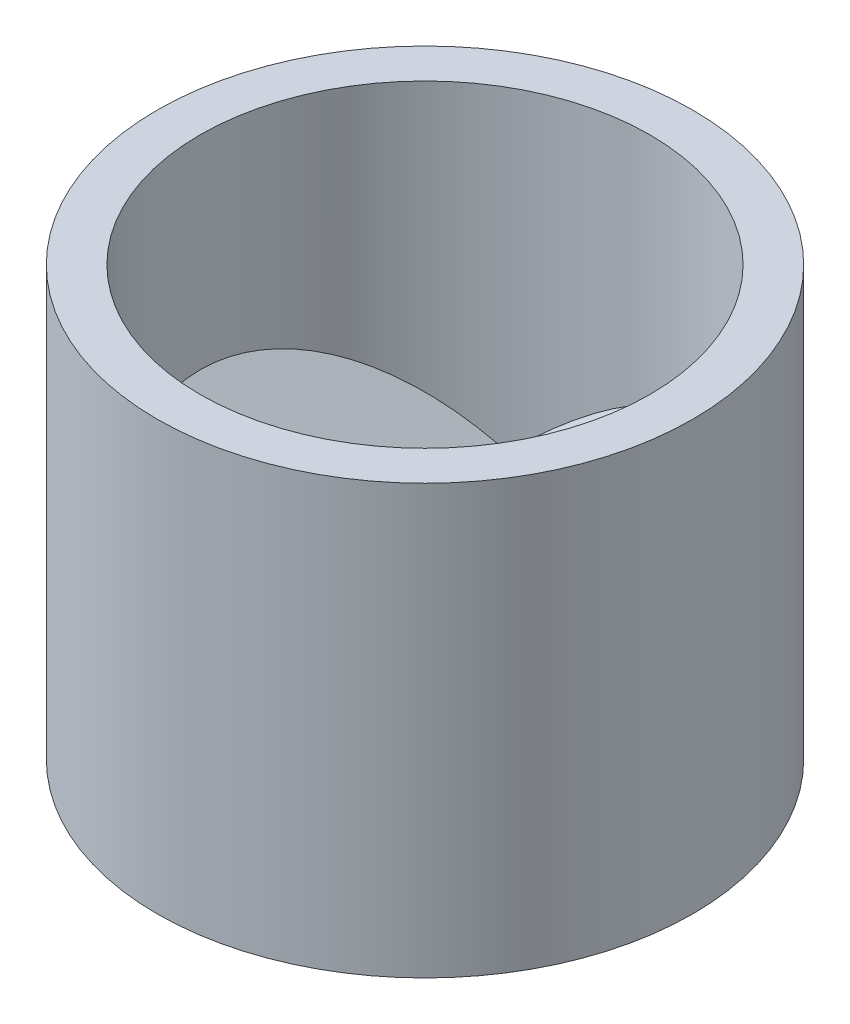
SolidWorks part; units mm, degrees
ref_plane "Front Plane" through (0, 0, 0) normal (0, 0, 1) x (1, 0, 0)
ref_plane "Top Plane" through (0, 0, 0) normal (0, 1, 0) x (1, 0, 0)
ref_plane "Right Plane" through (0, 0, 0) normal (1, 0, 0) x (0, 0, -1)
sketch "Sketch1" plane through (0, 0, 0) normal (0, 1, 0) x (1, 0, 0)
  circle A0 centre (0, 0) radius 12.5
  circle A1 centre (0, 0) radius 10.5
extrude "Boss-Extrude1" add sketch "Sketch1" along normal blind 20
sketch "Sketch2" plane through (0, 0, 0) normal (0, 1, 0) x (1, 0, 0)
  line L0 (0, 6.4855) -> (0, -5.2402)
ref_plane "Plane1" through (0, 0, 0) normal (0.7071, 0.7071, 0) x (0, 0, 1)
sketch "Sketch4" plane through (0, 0, 0) normal (0.7071, 0.7071, 0) x (0, 0, 1)
  line L0 (-9.3634, -8.1372) -> (0, -1.3221)
  line L1 (0, -1.3221) -> (9.5598, -8.0081)
  arc A0 (-9.3634, -8.1372) -> (9.5598, -8.0081) centre (0.0856, -6.2254) ccw
  point P4 (-9.3634, -8.1372)
  point P5 (9.5598, -8.0726)
extrude "Boss-Extrude2" add sketch "Sketch4" against normal blind 1
pattern_circular "CirPattern1" count 3 every 120 about axis through (0, 0, 0) along (0, 1, 0) of "Boss-Extrude2"
